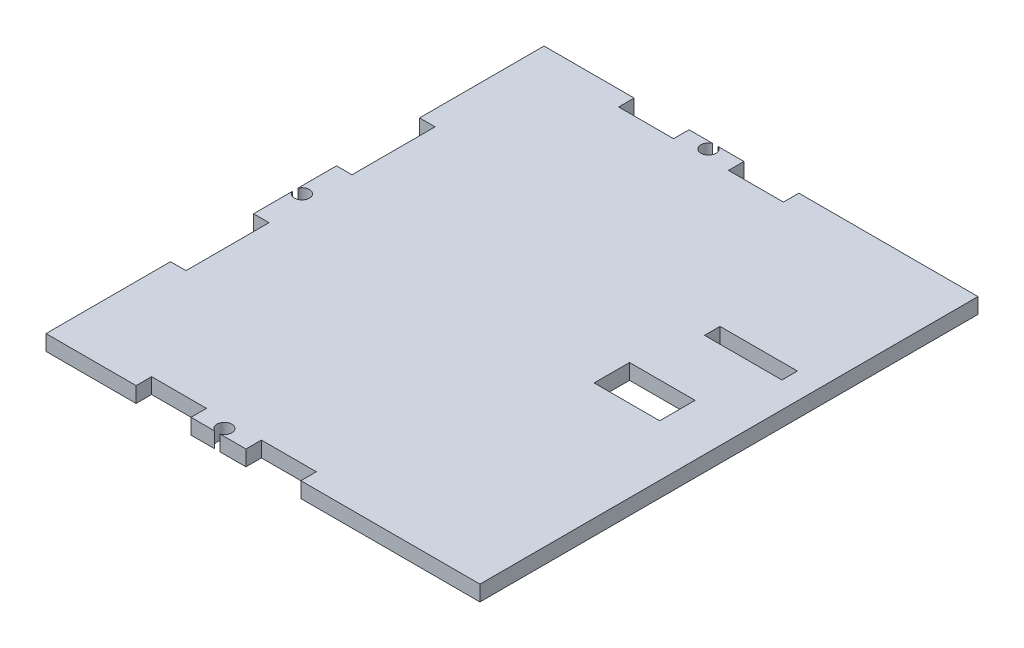
SolidWorks part; units mm, degrees
ref_plane "Front Plane" through (0, 0, 0) normal (0, 0, 1) x (1, 0, 0)
ref_plane "Top Plane" through (0, 0, 0) normal (0, 1, 0) x (1, 0, 0)
ref_plane "Right Plane" through (0, 0, 0) normal (1, 0, 0) x (0, 0, -1)
sketch "Sketch1" plane through (0, 0, 0) normal (0, 1, 0) x (1, 0, 0)
  line L1 (-33.425, 48.26) -> (33.425, 48.26)
  line L2 (-33.425, 48.26) -> (-33.425, -48.26)
  line L3 (-33.425, -48.26) -> (33.425, -48.26)
  line L4 (33.425, 48.26) -> (33.425, -48.26)
  line L5 (-33.425, 48.26) -> (33.425, -48.26) construction
  line L6 (-33.425, -48.26) -> (33.425, 48.26) construction
  point P0 (0, 0)
  dimension "D1" = 66.85
  dimension "D2" = 96.52
extrude "Boss-Extrude2" add sketch "Sketch1" along normal blind 3
sketch "Sketch2" plane through (0, 0, 48.26) normal (0, 0, 1) x (1, 0, 0)
  line L5 (-33.425, 3) -> (33.425, 3) construction
  line L6 (-33.425, 0) -> (33.425, 0) construction
  line L11 (-15.9625, 3) -> (15.9625, 3)
  line L12 (-15.9625, 3) -> (-15.9625, 0)
  line L13 (-15.9625, 0) -> (15.9625, 0)
  line L14 (15.9625, 3) -> (15.9625, 0)
  point P4 (0, 0)
  point P5 (0, 0)
  dimension "D1" = 31.925
extrude "Cut-Extrude1" cut sketch "Sketch2" against normal blind 3
mirror "Mirror1" about plane through (0, 0, 0) normal (0, 0, 1) of "Cut-Extrude1"
sketch "Sketch3" plane through (-33.425, 0, 0) normal (-1, 0, 0) x (0, 0, 1)
  line L0 (-48.26, 3) -> (48.26, 3) construction
  line L10 (-24.13, 3) -> (24.13, 3)
  line L11 (-24.13, 3) -> (-24.13, 0)
  line L12 (-24.13, 0) -> (24.13, 0)
  line L13 (24.13, 3) -> (24.13, 0)
  point P0 (0, 0)
  dimension "D1" = 48.26
extrude "Cut-Extrude2" cut sketch "Sketch3" against normal blind 3 contours L12 L13 L10 L11
sketch "Sketch4" plane through (0, 0, 45.26) normal (0, 0, 1) x (1, 0, 0)
  line L0 (-15.9625, 0) -> (15.9625, 0) construction
  line L1 (-5.3217, 0) -> (5.3217, 0)
  line L2 (-5.3217, 0) -> (-5.3217, 3)
  line L3 (-5.3217, 3) -> (5.3217, 3)
  line L4 (5.3217, 0) -> (5.3217, 3)
  line L5 (15.9625, 3) -> (-15.9625, 3) construction
  point P6 (0, 3)
  point P9 (0, 3)
  dimension "D1" = 10.6433
extrude "Boss-Extrude3" add sketch "Sketch4" along normal blind 3
mirror "Mirror2" about plane through (0, 0, 0) normal (0, 0, 1) of "Boss-Extrude3"
sketch "Sketch5" plane through (-30.425, 0, 0) normal (-1, 0, 0) x (0, 0, 1)
  line L0 (-24.13, 3) -> (24.13, 3) construction
  line L1 (-8.0433, 3) -> (8.0433, 3)
  line L2 (-8.0433, 3) -> (-8.0433, 0)
  line L3 (-8.0433, 0) -> (8.0433, 0)
  line L4 (8.0433, 3) -> (8.0433, 0)
  point P6 (0, 0)
  dimension "D1" = 16.0867
extrude "Boss-Extrude4" add sketch "Sketch5" along normal blind 3
sketch "Sketch6" plane through (0, 3, 0) normal (0, 1, 0) x (1, 0, 0)
  line L0 (-33.425, -8.0433) -> (-33.425, 8.0433) construction
  line L1 (-30.425, 1.5) -> (-33.525, 1.5)
  line L2 (-30.425, 1.5) -> (-30.425, -1.5)
  line L3 (-30.425, -1.5) -> (-33.525, -1.5)
  line L4 (-33.525, 1.5) -> (-33.525, -1.5)
  line L5 (-30.425, 0) -> (-32.075, 0) construction
  circle A0 centre (-32.075, 0) radius 1.45
  point P6 (-33.425, 0)
  point P7 (-33.525, 0)
  dimension "D3" = 2.9
  dimension "D1" = 3
  dimension "D2" = 3.1
extrude "Cut-Extrude10" cut sketch "Sketch6" against normal blind 3 contours A0
sketch "Sketch7" plane through (0, 3, 0) normal (0, 1, 0) x (1, 0, 0)
  line L1 (1.288, -48.36) -> (-1.712, -48.36)
  line L2 (1.288, -48.36) -> (1.288, -45.26)
  line L3 (1.288, -45.26) -> (-1.712, -45.26)
  line L4 (-1.712, -48.36) -> (-1.712, -45.26)
  circle A0 centre (-0.212, -46.91) radius 1.45
  dimension "D3" = 2.9
  dimension "D1" = 3
  dimension "D2" = 3.1
extrude "Cut-Extrude11" cut sketch "Sketch7" against normal blind 3 contours A0
mirror "Mirror3" about plane through (0, 0, 0) normal (0, 0, 1) of "Cut-Extrude11"
sketch "Sketch9" plane through (33.425, 0, 0) normal (1, 0, 0) x (0, 0, -1)
  line L1 (48.26, 0) -> (-48.26, 0)
  line L2 (48.26, 0) -> (48.26, 3)
  line L3 (48.26, 3) -> (-48.26, 3)
  line L4 (-48.26, 0) -> (-48.26, 3)
extrude "Boss-Extrude5" add sketch "Sketch9" along normal blind 17.25
sketch "Sketch10" plane through (0, 0, 0) normal (0, -1, 0) x (1, 0, 0)
  line L0 (50.675, 48.26) -> (50.675, -48.26) construction
  line L1 (27.975, 3.43) -> (40.675, 3.43)
  line L2 (27.975, 3.43) -> (27.975, -3.43)
  line L3 (27.975, -3.43) -> (40.675, -3.43)
  line L4 (40.675, 3.43) -> (40.675, -3.43)
  point P6 (40.675, 0)
  point P7 (50.675, 0)
  dimension "D1" = 6.86
  dimension "D2" = 12.7
  dimension "D3" = 10
extrude "Cut-Extrude12" cut sketch "Sketch10" against normal blind 3
sketch "Sketch12" plane through (0, 0, 0) normal (0, -1, 0) x (1, 0, 0)
  line L0 (-33.425, -48.26) -> (-33.425, -24.13) construction
  line L1 (30.675, -15.26) -> (45.675, -15.26)
  line L2 (30.675, -15.26) -> (30.675, -18.26)
  line L3 (30.675, -18.26) -> (45.675, -18.26)
  line L4 (45.675, -15.26) -> (45.675, -18.26)
  line L5 (50.675, -48.26) -> (15.9625, -48.26) construction
  dimension "D1" = 3
  dimension "D2" = 15
  dimension "D3" = 79.1
  dimension "D4" = 30
extrude "Cut-Extrude14" cut sketch "Sketch12" against normal blind 3
